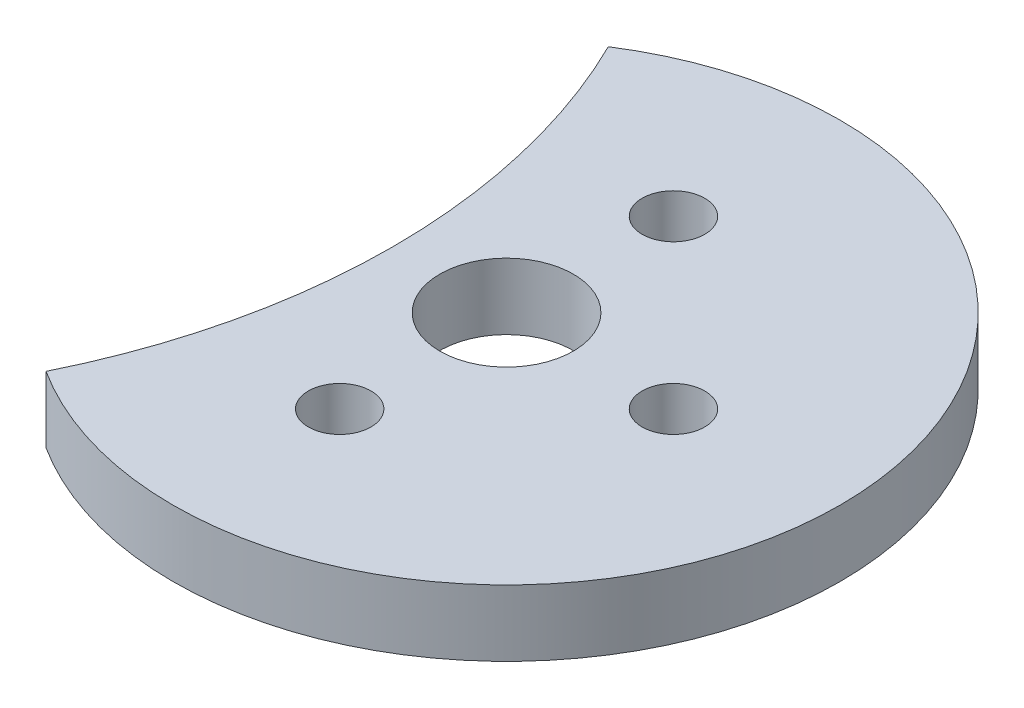
SolidWorks part; units mm, degrees
ref_plane "Front Plane" through (0, 0, 0) normal (0, 0, 1) x (1, 0, 0)
ref_plane "Top Plane" through (0, 0, 0) normal (0, 1, 0) x (1, 0, 0)
ref_plane "Right Plane" through (0, 0, 0) normal (1, 0, 0) x (0, 0, -1)
sketch "Sketch1" plane through (0, 0, 0) normal (0, 1, 0) x (1, 0, 0)
  circle A0 centre (0, 0) radius 15.9883
  dimension "D1" = 31.9766
extrude "Boss-Extrude1" add sketch "Sketch1" along normal blind 3.175
sketch "Sketch2" plane through (0, 3.175, 0) normal (0, 1, 0) x (1, 0, 0)
  line L0 (0, 0) -> (-5.459, 0) construction
  line L1 (-5.459, 0) -> (-35.939, 0) construction
  circle A0 centre (-35.939, 0) radius 30.48
  dimension "D2" = 60.96
  dimension "D1" = 5.459
extrude "Cut-Extrude1" cut sketch "Sketch2" against normal through all
ref_plane "Plane1" through (-8.6008, 3.175, -13.4778) normal (-0.843, 0, 0.5379) x (0.5379, 0, 0.843)
sketch "Sketch4" plane through (0, 3.175, 0) normal (0, 1, 0) x (1, 0, 0)
  line L0 (0, 8) -> (0, -8) construction
  line L1 (8, 0) -> (-8, 0) construction
  circle A0 centre (0, 0) radius 8 construction
  circle A1 centre (0, 8) radius 1.5
  circle A2 centre (0, -8) radius 1.5
  circle A3 centre (8, 0) radius 1.5
  circle A4 centre (0, 0) radius 3.2004
  dimension "D1" = 16
  dimension "D2" = 3
  dimension "D3" = 3
  dimension "D4" = 3
  dimension "D5" = 6.4008
extrude "Cut-Extrude2" cut sketch "Sketch4" against normal through all
